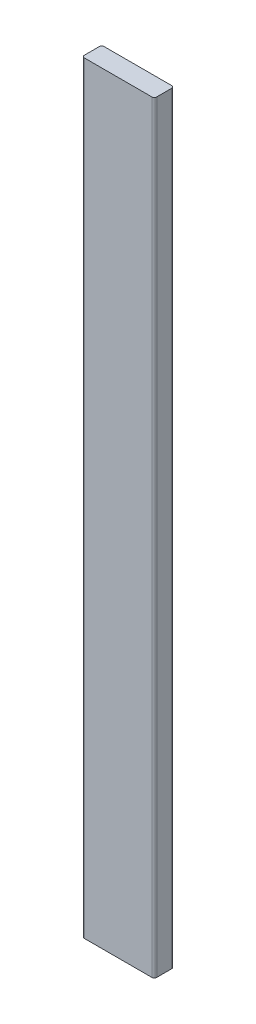
SolidWorks part; units mm, degrees
material "Pine"
ref_plane "Front Plane" through (0, 0, 0) normal (0, 0, 1) x (1, 0, 0)
ref_plane "Top Plane" through (0, 0, 0) normal (0, 1, 0) x (1, 0, 0)
ref_plane "Right Plane" through (0, 0, 0) normal (1, 0, 0) x (0, 0, -1)
sketch "Sketch1" plane through (0, 0, 0) normal (0, 0, 1) x (1, 0, 0)
  line L0 (-781.7306, 0) -> (-204.9322, 0) construction
  line L1 (-344.6322, 1473.2) -> (-204.9322, 1473.2)
  line L2 (-344.6322, 1473.2) -> (-344.6322, 0)
  line L3 (-344.6322, 0) -> (-204.9322, 0)
  line L4 (-204.9322, 1473.2) -> (-204.9322, 0)
  line L5 (-204.9322, 440.5504) -> (-204.9322, 754.7501) construction
extrude "Boss-Extrude1" add sketch "Sketch1" against normal up to surface (38.1 mm away)
fillet "Fillet1" radius 4.7625 4 edges at (-344.6322, 736.6, 0) (-204.9322, 736.6, -38.1) (-344.6322, 736.6, -38.1) (-204.9322, 736.6, 0)
ref_plane "Plane1" through (-274.7822, 0, 0) normal (1, 0, 0) x (0, 0, -1)
